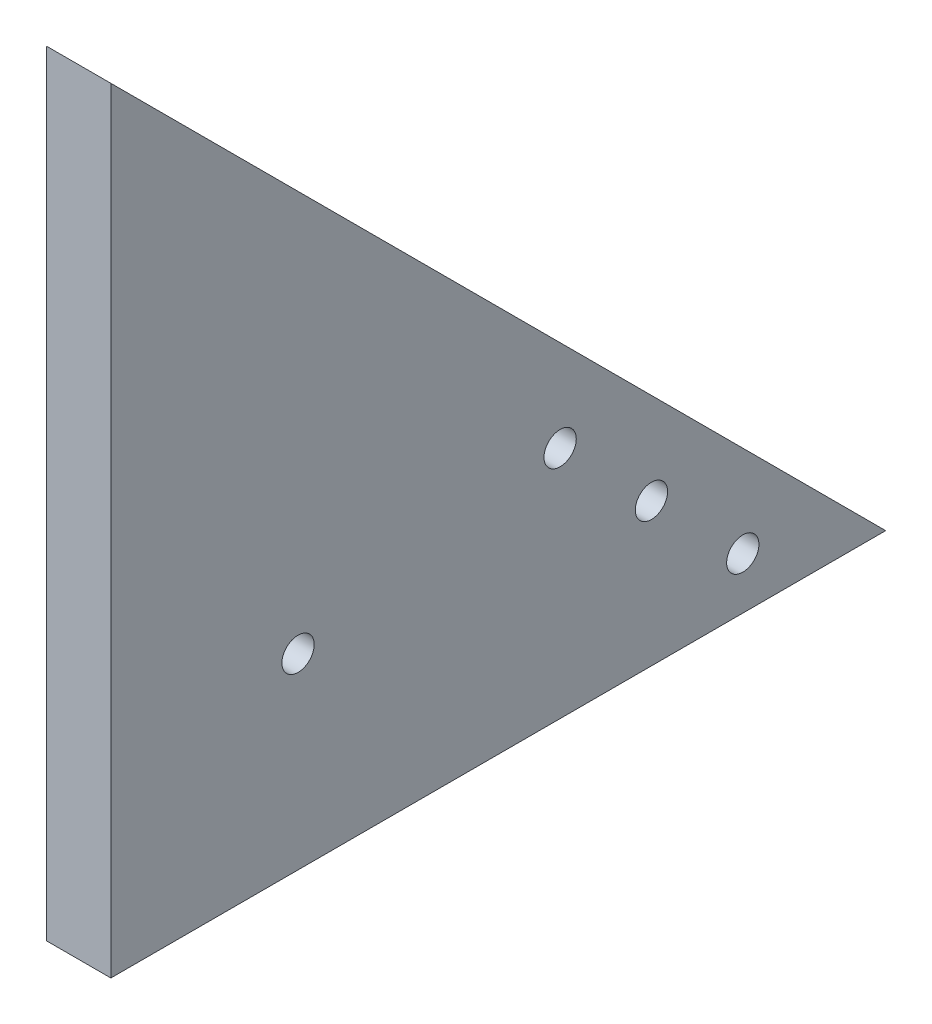
SolidWorks part; units mm, degrees
ref_plane "Front Plane" through (0, 0, 0) normal (0, 0, 1) x (1, 0, 0)
ref_plane "Top Plane" through (0, 0, 0) normal (0, 1, 0) x (1, 0, 0)
ref_plane "Right Plane" through (0, 0, 0) normal (1, 0, 0) x (0, 0, -1)
sketch "Sketch1" plane through (0, 0, 0) normal (1, 0, 0) x (0, 0, -1)
  line L0 (0, 0) -> (0, 120)
  line L2 (0, 0) -> (120, 0)
  line L4 (120, 0) -> (0, 120)
  dimension "D1" = 120
  dimension "D2" = 120
extrude "Boss-Extrude1" add sketch "Sketch1" along normal blind 10
sketch "Sketch4" plane through (10, 0, 0) normal (1, 0, 0) x (0, 0, -1)
  line L0 (0, 0) -> (31.0179, 31.0179) construction
  line L1 (120, 0) -> (0, 120) construction
  circle A0 centre (83.7206, 22.1372) radius 2.5
  circle A1 centre (97.8628, 7.9951) radius 2.5
  circle A2 centre (69.5785, 36.2794) radius 2.5
  circle A3 centre (28.9914, 28.9914) radius 2.5
  dimension "D1" = 20
  dimension "D6" = 41
  dimension "D2" = 20
  dimension "D3" = 10
  dimension "D4" = 10
  dimension "D5" = 10
  dimension "D7" = 42.5
extrude "Cut-Extrude3" cut sketch "Sketch4" against normal blind 10
